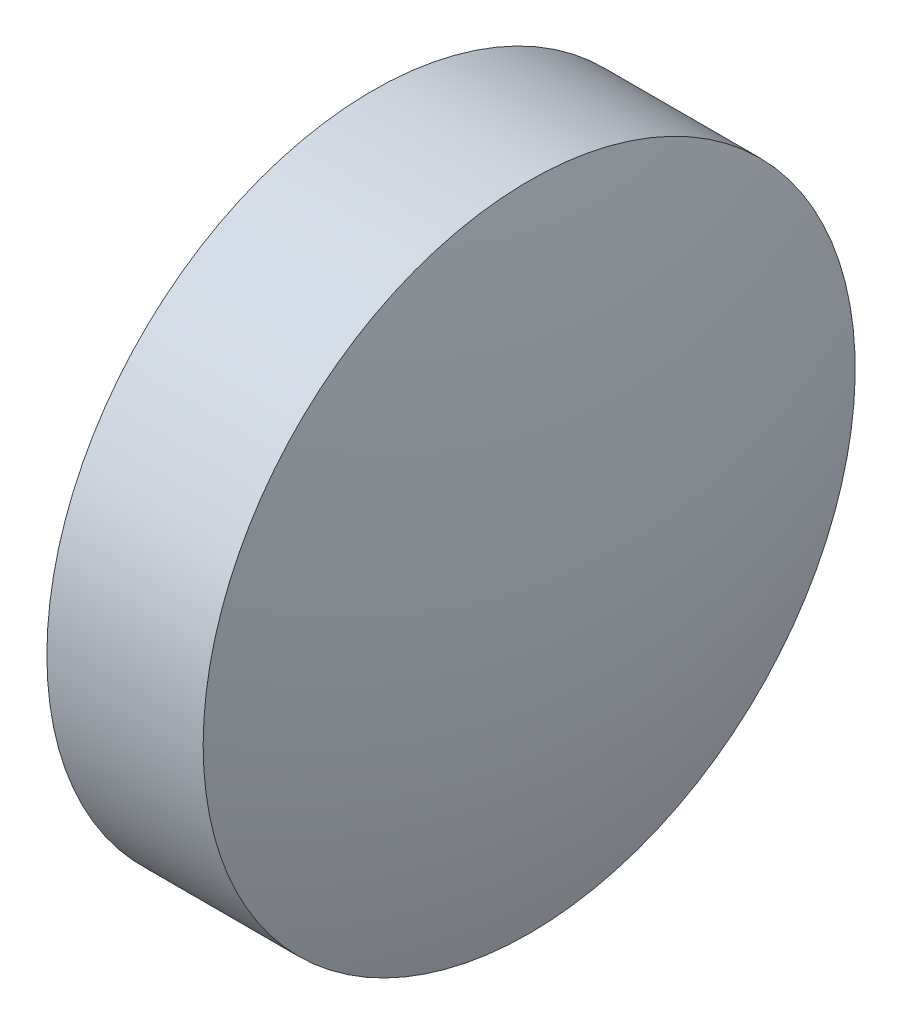
SolidWorks part; units mm, degrees
ref_plane "前视基准面" through (0, 0, 0) normal (0, 0, 1) x (1, 0, 0)
ref_plane "上视基准面" through (0, 0, 0) normal (0, 1, 0) x (1, 0, 0)
ref_plane "右视基准面" through (0, 0, 0) normal (1, 0, 0) x (0, 0, -1)
sketch "草图1" plane through (0, 0, 0) normal (0, 0, 1) x (1, 0, 0)
  line L0 (606.2759, -17.2012) -> (611.671, -17.2012) construction
  line L1 (607.0816, -17.2012) -> (607.0816, -14.0512)
  line L2 (609.0816, -17.2012) -> (607.0816, -17.2012)
  line L5 (607.0816, -14.0512) -> (608.5916, -14.0512)
  arc A0 (609.0816, -17.2012) -> (608.5916, -14.0512) centre (598.7116, -17.2012) ccw
revolve "旋转1" add sketch "草图1" angle 360 about L0
